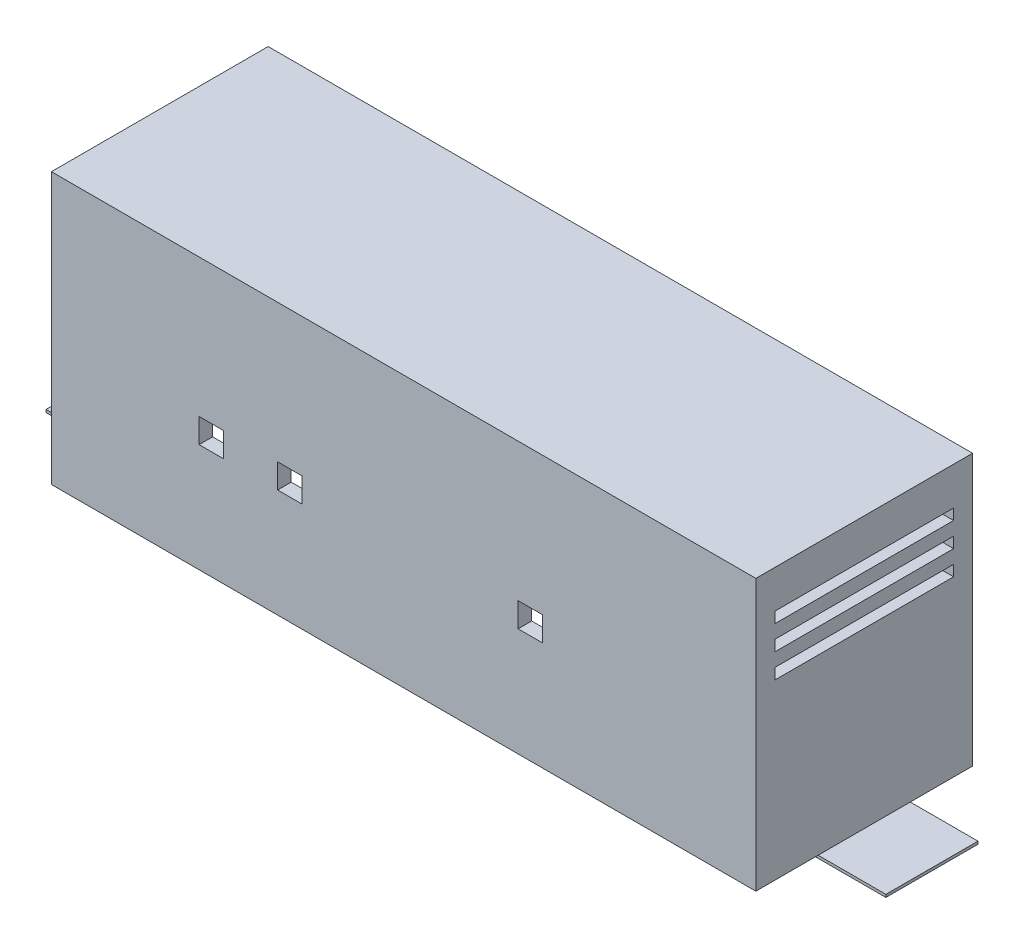
SolidWorks part; units mm, degrees
ref_plane "Front Plane" through (0, 0, 0) normal (0, 0, 1) x (1, 0, 0)
ref_plane "Top Plane" through (0, 0, 0) normal (0, 1, 0) x (1, 0, 0)
ref_plane "Right Plane" through (0, 0, 0) normal (1, 0, 0) x (0, 0, -1)
sketch "Sketch1" plane through (0, 0, 0) normal (0, 1, 0) x (1, 0, 0)
  line L1 (130, 40) -> (-130, 40)
  line L2 (130, 40) -> (130, -40)
  line L3 (130, -40) -> (-130, -40)
  line L4 (-130, 40) -> (-130, -40)
  line L5 (130, 40) -> (-130, -40) construction
  line L6 (130, -40) -> (-130, 40) construction
  point P0 (0, 0)
extrude "Boss-Extrude1" add sketch "Sketch1" along normal blind 100
sketch "Sketch2" plane through (0, 0, 0) normal (0, -1, 0) x (1, 0, 0)
  line L0 (-130, -40) -> (-130, 40) construction
  line L1 (125, -35) -> (-125, -35)
  line L2 (125, -35) -> (125, 35)
  line L3 (125, 35) -> (-125, 35)
  line L4 (-125, -35) -> (-125, 35)
  line L5 (125, -35) -> (-125, 35) construction
  line L6 (125, 35) -> (-125, -35) construction
  line L8 (-130, 40) -> (130, 40) construction
  point P0 (0, 0)
  dimension "D1" = 5
  dimension "D2" = 5
extrude "inside" cut sketch "Sketch2" against normal offset from surface (90 mm away) 10 contours L2 L1 L4 L3 up to face at (0, 100, 0)
sketch "Sketch8" plane through (0, 0, 40) normal (0, 0, 1) x (1, 0, 0)
  line L0 (-130, 100) -> (-130, 0) construction
  line L1 (-75.5, 49) -> (-66.5, 49)
  line L2 (-75.5, 49) -> (-75.5, 40)
  line L3 (-75.5, 40) -> (-66.5, 40)
  line L4 (-66.5, 49) -> (-66.5, 40)
  line L5 (-75.5, 49) -> (-66.5, 40) construction
  line L6 (-75.5, 40) -> (-66.5, 49) construction
  line L7 (-130, 0) -> (130, 0) construction
  line L8 (-46.5, 49) -> (-37.5, 49)
  line L9 (-46.5, 49) -> (-46.5, 40)
  line L10 (-46.5, 40) -> (-37.5, 40)
  line L11 (-37.5, 49) -> (-37.5, 40)
  line L12 (-46.5, 49) -> (-37.5, 40) construction
  line L13 (-46.5, 40) -> (-37.5, 49) construction
  line L14 (130, 100) -> (130, 0) construction
  line L15 (51.25, 49) -> (42.25, 49)
  line L16 (51.25, 49) -> (51.25, 40)
  line L17 (51.25, 40) -> (42.25, 40)
  line L18 (42.25, 49) -> (42.25, 40)
  line L19 (51.25, 49) -> (42.25, 40) construction
  line L20 (51.25, 40) -> (42.25, 49) construction
  point P0 (-71, 44.5)
  point P9 (-42, 44.5)
  point P14 (46.75, 44.5)
  dimension "D1" = 54.5
  dimension "D2" = 40
  dimension "D3" = 40
  dimension "D4" = 83.5
  dimension "D5" = 40
  dimension "D6" = 87.75
extrude "Wire holes" cut sketch "Sketch8" against normal blind 23
sketch "Sketch12" plane through (130, 0, 0) normal (1, 0, 0) x (0, 0, -1)
  line L0 (40, 100) -> (40, 0) construction
  line L1 (-33, 86) -> (33, 86)
  line L2 (-33, 86) -> (-33, 82)
  line L3 (-33, 82) -> (33, 82)
  line L4 (33, 86) -> (33, 82)
  line L5 (-33, 86) -> (33, 82) construction
  line L6 (-33, 82) -> (33, 86) construction
  line L7 (-40, 100) -> (-40, 0) construction
  line L9 (-40, 100) -> (40, 100) construction
  point P0 (0, 84)
  dimension "D1" = 7
  dimension "D2" = 7
  dimension "D3" = 4
  dimension "D4" = 14
extrude "Ventalation" cut sketch "Sketch12" against normal blind 15
sketch "Sketch14" plane through (130, 0, 0) normal (1, 0, 0) x (0, 0, -1)
  line L1 (-33, 77) -> (33, 77)
  line L2 (-33, 77) -> (-33, 73)
  line L3 (-33, 73) -> (33, 73)
  line L4 (33, 77) -> (33, 73)
  line L5 (-33, 77) -> (33, 73) construction
  line L6 (-33, 73) -> (33, 77) construction
  line L7 (-40, 100) -> (-40, 0) construction
  line L8 (40, 100) -> (40, 0) construction
  line L9 (-33, 82) -> (33, 82) construction
  point P0 (0, 75)
  dimension "D1" = 7
  dimension "D2" = 7
  dimension "D3" = 4
  dimension "D4" = 5
extrude "Ventalation 2" cut sketch "Sketch14" against normal blind 10
sketch "Sketch16" plane through (130, 0, 0) normal (1, 0, 0) x (0, 0, -1)
  line L0 (-40, 100) -> (-40, 0) construction
  line L1 (-33, 68) -> (33, 68)
  line L2 (-33, 68) -> (-33, 64)
  line L3 (-33, 64) -> (33, 64)
  line L4 (33, 68) -> (33, 64)
  line L5 (-33, 68) -> (33, 64) construction
  line L6 (-33, 64) -> (33, 68) construction
  line L7 (40, 100) -> (40, 0) construction
  line L8 (-33, 73) -> (33, 73) construction
  point P0 (0, 66)
  dimension "D1" = 7
  dimension "D2" = 7
  dimension "D3" = 5
  dimension "D4" = 4
extrude "Ventalation 3" cut sketch "Sketch16" against normal blind 10
sketch "Sketch20" plane through (0, 0, 0) normal (0, -1, 0) x (1, 0, 0)
  line L0 (-125, -35) -> (-125, 35) construction
  line L1 (-17, -35) -> (17, -35)
  line L2 (-17, -35) -> (-17, -65)
  line L3 (-17, -65) -> (17, -65)
  line L4 (17, -35) -> (17, -65)
  line L5 (-17, -35) -> (17, -65) construction
  line L6 (-17, -65) -> (17, -35) construction
  line L7 (-125, -35) -> (125, -35) construction
  line L9 (125, -35) -> (125, 35) construction
  point P0 (0, -50)
  point P7 (0, 0)
  dimension "D1" = 108
  dimension "D2" = 108
extrude "Command Strip front" add sketch "Sketch20" along normal blind 1
sketch "Sketch21" plane through (0, 0, 0) normal (0, -1, 0) x (1, 0, 0)
  line L0 (-125, -35) -> (-125, 35) construction
  line L1 (-125, 17) -> (-155, 17)
  line L2 (-125, 17) -> (-125, -17)
  line L3 (-125, -17) -> (-155, -17)
  line L4 (-155, 17) -> (-155, -17)
  line L5 (-125, 17) -> (-155, -17) construction
  line L6 (-125, -17) -> (-155, 17) construction
  line L7 (-125, 35) -> (125, 35) construction
  line L8 (-17, -35) -> (-125, -35) construction
  point P0 (-140, 0)
  dimension "D1" = 18
  dimension "D2" = 18
extrude "Command strip right" add sketch "Sketch21" along normal blind 1
sketch "Sketch22" plane through (0, 0, 0) normal (0, -1, 0) x (1, 0, 0)
  line L0 (125, 33) -> (125, -33) construction
  line L1 (125, 17) -> (155, 17)
  line L2 (125, 17) -> (125, -17)
  line L3 (125, -17) -> (155, -17)
  line L4 (155, 17) -> (155, -17)
  line L5 (125, 17) -> (155, -17) construction
  line L6 (125, -17) -> (155, 17) construction
  line L7 (-125, 35) -> (125, 35) construction
  line L8 (-125, -35) -> (125, -35) construction
  point P0 (140, 0)
  dimension "D1" = 18
  dimension "D2" = 18
extrude "Boss-Extrude4" add sketch "Sketch22" along normal blind 1
